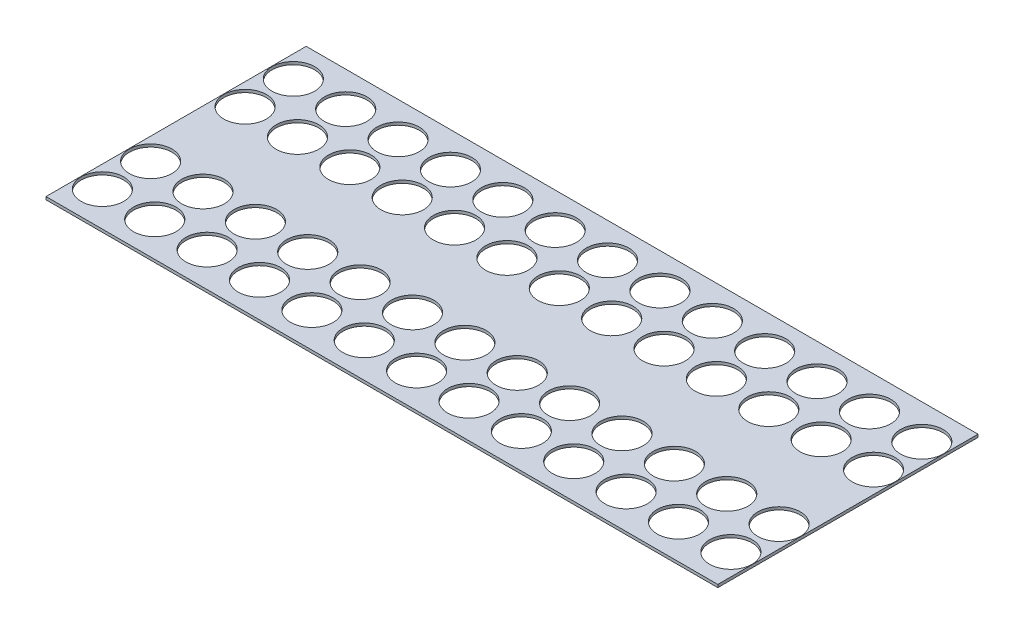
SolidWorks part; units mm, degrees
material "Balsa"
ref_plane "Front Plane" through (0, 0, 0) normal (0, 0, 1) x (1, 0, 0)
ref_plane "Top Plane" through (0, 0, 0) normal (0, 1, 0) x (1, 0, 0)
ref_plane "Right Plane" through (0, 0, 0) normal (1, 0, 0) x (0, 0, -1)
sketch "Sketch1" plane through (0, 0, 0) normal (0, 1, 0) x (1, 0, 0)
  line L1 (710, 137.5) -> (0, 137.5)
  line L2 (710, 137.5) -> (710, -137.5)
  line L3 (710, -137.5) -> (0, -137.5)
  line L4 (0, 137.5) -> (0, -137.5)
  circle A3 centre (23, 100.9) radius 22.5
  circle A4 centre (23, 49.9) radius 22.5
  circle A5 centre (23, -49.9) radius 22.5
  circle A6 centre (23, -100.9) radius 22.5
  circle A7 centre (78.35, 100.9) radius 22.5
  circle A8 centre (78.35, 49.9) radius 22.5
  circle A9 centre (78.35, -49.9) radius 22.5
  circle A10 centre (78.35, -100.9) radius 22.5
  circle A11 centre (133.7, 100.9) radius 22.5
  circle A12 centre (133.7, 49.9) radius 22.5
  circle A13 centre (133.7, -49.9) radius 22.5
  circle A14 centre (133.7, -100.9) radius 22.5
  circle A15 centre (189.05, 100.9) radius 22.5
  circle A16 centre (189.05, 49.9) radius 22.5
  circle A17 centre (189.05, -49.9) radius 22.5
  circle A18 centre (189.05, -100.9) radius 22.5
  circle A19 centre (244.4, 100.9) radius 22.5
  circle A20 centre (244.4, 49.9) radius 22.5
  circle A21 centre (244.4, -49.9) radius 22.5
  circle A22 centre (244.4, -100.9) radius 22.5
  circle A23 centre (299.75, 100.9) radius 22.5
  circle A24 centre (299.75, 49.9) radius 22.5
  circle A25 centre (299.75, -49.9) radius 22.5
  circle A26 centre (299.75, -100.9) radius 22.5
  circle A27 centre (355.1, 100.9) radius 22.5
  circle A28 centre (355.1, 49.9) radius 22.5
  circle A29 centre (355.1, -49.9) radius 22.5
  circle A30 centre (355.1, -100.9) radius 22.5
  circle A31 centre (410.45, 100.9) radius 22.5
  circle A32 centre (410.45, 49.9) radius 22.5
  circle A33 centre (410.45, -49.9) radius 22.5
  circle A34 centre (410.45, -100.9) radius 22.5
  circle A35 centre (465.8, 100.9) radius 22.5
  circle A36 centre (465.8, 49.9) radius 22.5
  circle A37 centre (465.8, -49.9) radius 22.5
  circle A38 centre (465.8, -100.9) radius 22.5
  circle A39 centre (521.15, 100.9) radius 22.5
  circle A40 centre (521.15, 49.9) radius 22.5
  circle A41 centre (521.15, -49.9) radius 22.5
  circle A42 centre (521.15, -100.9) radius 22.5
  circle A43 centre (576.5, 100.9) radius 22.5
  circle A44 centre (576.5, 49.9) radius 22.5
  circle A45 centre (576.5, -49.9) radius 22.5
  circle A46 centre (576.5, -100.9) radius 22.5
  circle A47 centre (631.85, 100.9) radius 22.5
  circle A48 centre (631.85, 49.9) radius 22.5
  circle A49 centre (631.85, -49.9) radius 22.5
  circle A50 centre (631.85, -100.9) radius 22.5
  circle A51 centre (687.2, 100.9) radius 22.5
  circle A52 centre (687.2, 49.9) radius 22.5
  circle A53 centre (687.2, -49.9) radius 22.5
  circle A54 centre (687.2, -100.9) radius 22.5
  point P0 (440.1807, 0)
  point P13 (0, 0)
  dimension "D1" = 45
  dimension "D2" = 45
  dimension "D3" = 45
  dimension "D4" = 45
  dimension "D5" = 51
  dimension "D6" = 99.8
  dimension "D7" = 51
  dimension "D8" = 49.9
  dimension "D9" = 275
  dimension "D11" = 55.35
  dimension "D12" = 23
  dimension "D13" = 710
  dimension "D10" = 13
extrude "Boss-Extrude1" add sketch "Sketch1" along normal blind 3
equation "\"D2@Sketch1\"=\"D1@Sketch1\""
equation "\"D3@Sketch1\"=\"D1@Sketch1\""
equation "\"D4@Sketch1\"=\"D1@Sketch1\""
equation "\"D7@Sketch1\"=\"D5@Sketch1\""
equation "\"D8@Sketch1\"=\"D6@Sketch1\"/2"
